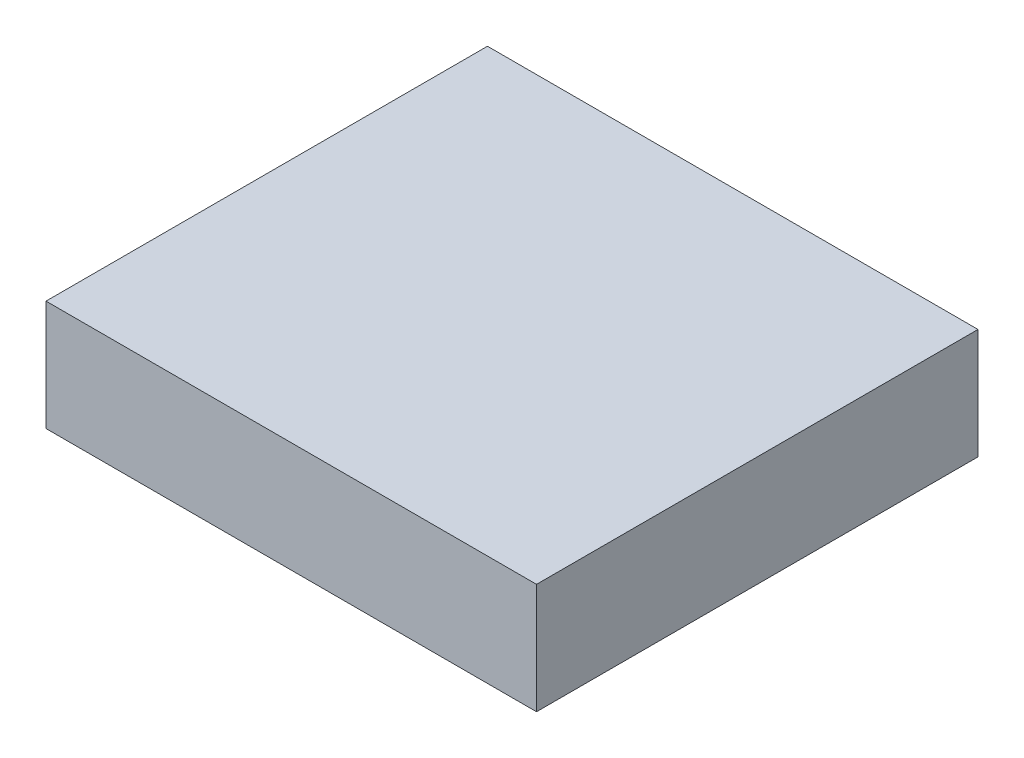
SolidWorks part; units mm, degrees
ref_plane "Front" through (0, 0, 0) normal (0, 0, 1) x (1, 0, 0)
ref_plane "Top" through (0, 0, 0) normal (0, 1, 0) x (1, 0, 0)
ref_plane "Right" through (0, 0, 0) normal (1, 0, 0) x (0, 0, -1)
sketch "Sketch1" plane through (0, 0, 0) normal (0, 1, 0) x (1, 0, 0)
  line L1 (0, 0) -> (100, 0)
  line L2 (0, 0) -> (0, 90)
  line L3 (0, 90) -> (100, 90)
  line L4 (100, 0) -> (100, 90)
  dimension "D1" = 100
  dimension "D2" = 90
extrude "Boss-Extrude1" add sketch "Sketch1" along normal blind 22.5
